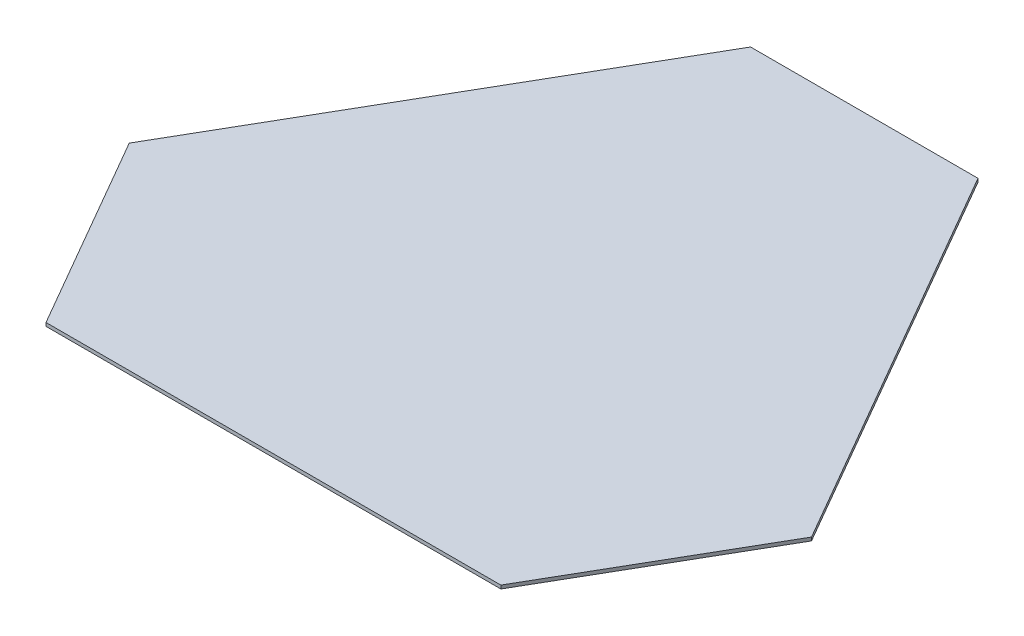
SolidWorks part; units mm, degrees
material "AISI 1020"
ref_plane "Front Plane" through (0, 0, 0) normal (0, 0, 1) x (1, 0, 0)
ref_plane "Top Plane" through (0, 0, 0) normal (0, 1, 0) x (1, 0, 0)
ref_plane "Right Plane" through (0, 0, 0) normal (1, 0, 0) x (0, 0, -1)
sketch "Sketch2" plane through (0, 0, 0) normal (0, 1, 0) x (1, 0, 0)
  line L0 (-100, 288.6751) -> (100, 288.6751)
  line L1 (100, 288.6751) -> (300, -57.735)
  line L2 (300, -57.735) -> (200, -230.9401)
  line L3 (200, -230.9401) -> (-200, -230.9401)
  line L4 (-200, -230.9401) -> (-300, -57.735)
  line L5 (-300, -57.735) -> (-100, 288.6751)
  line L6 (-250, -144.3376) -> (200, 115.4701)
  point P3 (0, 288.6751)
  dimension "D1" = 200
  dimension "D2" = 400
  dimension "D3" = 400
  dimension "D4" = 200
  dimension "D5" = 400
  dimension "D6" = 200
  dimension "D7" = 120
  dimension "D8" = 120
  dimension "D9" = 519.6152
  dimension "D10" = 0
  dimension "D11" = 90
extrude "Boss-Extrude1" add sketch "Sketch2" along normal blind 3 contours L4 L6 L1 L0 L5 | L6 L4 L3 L2 L1
